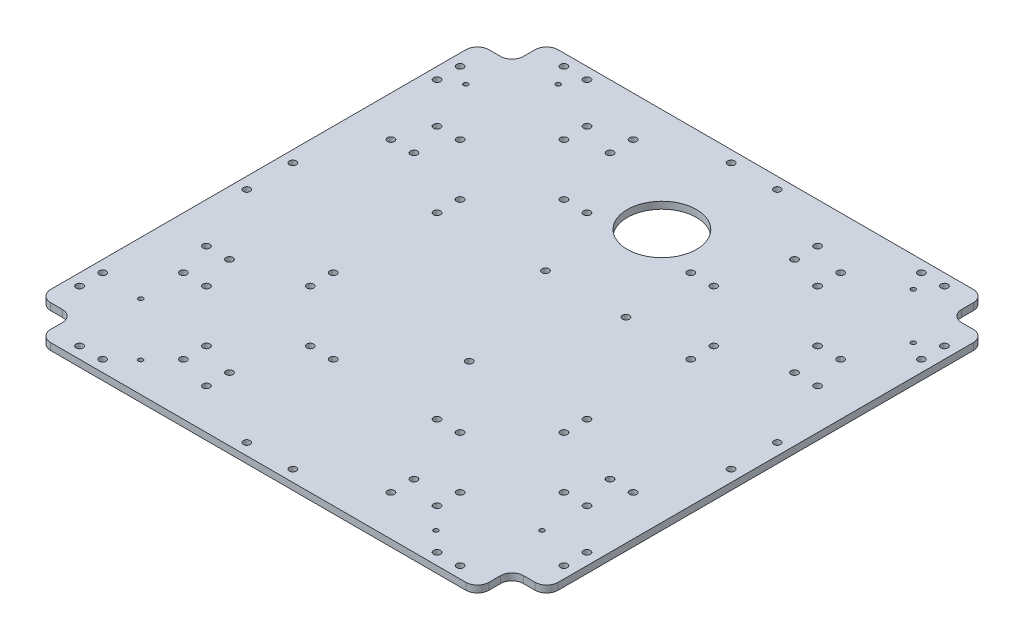
SolidWorks part; units mm, degrees
material "Polywood"
ref_plane "Спереди" through (0, 0, 0) normal (0, 0, 1) x (1, 0, 0)
ref_plane "Сверху" through (0, 0, 0) normal (0, 1, 0) x (1, 0, 0)
ref_plane "Справа" through (0, 0, 0) normal (1, 0, 0) x (0, 0, -1)
sketch "Эскиз1" plane through (0, 0, 0) normal (0, 1, 0) x (1, 0, 0)
  line L1 (110, -110) -> (-110, -110)
  line L2 (110, -110) -> (110, 110)
  line L3 (110, 110) -> (-110, 110)
  line L4 (-110, -110) -> (-110, 110)
  line L5 (110, -110) -> (-110, 110) construction
  line L6 (110, 110) -> (-110, -110) construction
  line L7 (0, 0) -> (50000, 0) construction
  circle A32 centre (0, 65) radius 15
  point P0 (0, 0)
  dimension "D6" = 30
  dimension "D2" = 220
  dimension "D1" = 220
  dimension "D7" = 65
extrude "Бобышка-Вытянуть1" add sketch "Эскиз1" along normal blind 3
sketch "Эскиз2" plane through (0, 0, 0) normal (0, 0, 1) x (1, 0, 0)
  line L0 (0, 0) -> (0, 41.9945) construction
sketch "Эскиз3" plane through (0, 3, 0) normal (0, 1, 0) x (1, 0, 0)
  line L8 (0, 0) -> (0, -50000) construction
  line L9 (0, 0) -> (50000, 0) construction
  line L28 (110, 110) -> (110, 95)
  line L29 (-110, 110) -> (-95, 110)
  line L30 (-110, 110) -> (-110, 95)
  line L31 (-110, 95) -> (-95, 95)
  line L32 (-95, 110) -> (-95, 95)
  line L33 (110, 110) -> (95, 110)
  line L34 (95, 110) -> (95, 95)
  line L35 (110, 95) -> (95, 95)
  line L36 (110, -110) -> (95, -110)
  line L37 (110, -110) -> (110, -95)
  line L38 (110, -95) -> (95, -95)
  line L39 (95, -110) -> (95, -95)
  line L40 (-110, -110) -> (-110, -95)
  line L41 (-110, -110) -> (-95, -110)
  line L42 (-95, -110) -> (-95, -95)
  line L43 (-110, -95) -> (-95, -95)
  dimension "D1" = 15
extrude "Вырез-Вытянуть1" cut sketch "Эскиз3" against normal through all
fillet "Скругление1" radius 5 4 edges at (-95, 1.5, -95) (-95, 1.5, 95) (95, 1.5, 95) (95, 1.5, -95)
fillet "Скругление2" radius 5 8 edges at (95, 1.5, -110) (110, 1.5, -95) (110, 1.5, 95) (95, 1.5, 110) (-95, 1.5, -110) (-110, 1.5, -95) (-95, 1.5, 110) (-110, 1.5, 95)
sketch "Эскиз4" plane through (0, 3, 0) normal (0, 1, 0) x (1, 0, 0)
  line L1 (90, 110) -> (-90, 110) construction
  line L2 (-110, 90) -> (-110, -90) construction
  line L3 (-77.5, 104.7863) -> (-77.5, -49895.2137) construction
  line L4 (0, 0) -> (0, 50000) construction
  circle A36 centre (-82.5, 105) radius 1.5
  circle A37 centre (-72.5, 105) radius 1.5
  circle A38 centre (72.5, 105) radius 1.5
  circle A39 centre (82.5, 105) radius 1.5
  circle A40 centre (105, 82.5) radius 1.5
  circle A41 centre (105, 72.5) radius 1.5
  circle A42 centre (105, -72.5) radius 1.5
  circle A43 centre (105, -82.5) radius 1.5
  circle A44 centre (82.5, -105) radius 1.5
  circle A45 centre (72.5, -105) radius 1.5
  circle A46 centre (-72.5, -105) radius 1.5
  circle A47 centre (-82.5, -105) radius 1.5
  circle A48 centre (-105, -82.5) radius 1.5
  circle A49 centre (-105, -72.5) radius 1.5
  circle A50 centre (-105, 72.5) radius 1.5
  circle A51 centre (-105, 82.5) radius 1.5
  circle A52 centre (-10, 105) radius 1.5
  circle A53 centre (10, 105) radius 1.5
  circle A54 centre (105, 10) radius 1.5
  circle A55 centre (105, -10) radius 1.5
  circle A56 centre (10, -105) radius 1.5
  circle A57 centre (-10, -105) radius 1.5
  circle A58 centre (-105, -10) radius 1.5
  circle A59 centre (-105, 10) radius 1.5
  dimension "D1" = 3
  dimension "D2" = 5
  dimension "D3" = 27.5
  dimension "D4" = 5
  dimension "D6" = 10
  dimension "D5" = 4
  dimension "D7" = 4
extrude "Вырез-Вытянуть2" cut sketch "Эскиз4" against normal through all
sketch "Эскиз6" plane through (0, 3, 0) normal (0, 1, 0) x (1, 0, 0)
  line L0 (7.7, 41.6342) -> (7.7, -49958.3658) construction
  line L1 (-12.75, 27.25) -> (28.15, 27.25) construction
  line L2 (-12.75, 27.25) -> (-12.75, -29.25) construction
  line L3 (-12.75, -29.25) -> (28.15, -29.25) construction
  line L4 (28.15, 27.25) -> (28.15, -29.25) construction
  circle A0 centre (-9.75, 24.25) radius 1.5
  circle A1 centre (7.7, -26.25) radius 1.5
  circle A2 centre (25.15, 24.25) radius 1.5
  point P8 (7.7, 27.25)
  point P13 (0, 0)
  dimension "D3" = 3
  dimension "D7" = 27.25
  dimension "D1" = 40.9
  dimension "D2" = 56.5
  dimension "D4" = 3
  dimension "D5" = 17.45
  dimension "D6" = 50.5
  dimension "D8" = 12.75
extrude "MTi-680G holes" cut sketch "Эскиз6" against normal through all
sketch "Sketch1" plane through (0, 3, 0) normal (0, 1, 0) x (1, 0, 0)
  line L1 (55, -55) -> (-55, -55) construction
  line L2 (55, -55) -> (55, 55) construction
  line L3 (55, 55) -> (-55, 55) construction
  line L4 (-55, -55) -> (-55, 55) construction
  line L5 (55, -55) -> (-55, 55) construction
  line L6 (55, 55) -> (-55, -55) construction
  circle A0 centre (-55, 32.5) radius 1.5
  circle A1 centre (-55, 22.5) radius 1.5
  circle A20 centre (-77.5, 55) radius 1.5
  circle A21 centre (-87.5, 55) radius 1.5
  circle A22 centre (-55, 77.5) radius 1.5
  circle A23 centre (-55, 87.5) radius 1.5
  circle A24 centre (-32.5, 55) radius 1.5
  circle A25 centre (-22.5, 55) radius 1.5
  circle A26 centre (32.5, 55) radius 1.5
  circle A27 centre (22.5, 55) radius 1.5
  circle A28 centre (55, 77.5) radius 1.5
  circle A29 centre (55, 87.5) radius 1.5
  circle A30 centre (77.5, 55) radius 1.5
  circle A31 centre (87.5, 55) radius 1.5
  circle A32 centre (55, 32.5) radius 1.5
  circle A33 centre (55, 22.5) radius 1.5
  circle A34 centre (55, -32.5) radius 1.5
  circle A35 centre (55, -22.5) radius 1.5
  circle A36 centre (77.5, -55) radius 1.5
  circle A37 centre (87.5, -55) radius 1.5
  circle A38 centre (55, -77.5) radius 1.5
  circle A39 centre (55, -87.5) radius 1.5
  circle A40 centre (32.5, -55) radius 1.5
  circle A41 centre (22.5, -55) radius 1.5
  circle A42 centre (-32.5, -55) radius 1.5
  circle A43 centre (-22.5, -55) radius 1.5
  circle A44 centre (-55, -77.5) radius 1.5
  circle A45 centre (-55, -87.5) radius 1.5
  circle A46 centre (-77.5, -55) radius 1.5
  circle A47 centre (-87.5, -55) radius 1.5
  circle A48 centre (-55, -32.5) radius 1.5
  circle A49 centre (-55, -22.5) radius 1.5
  point P0 (0, 0)
  dimension "D5" = 3
  dimension "D1" = 110
  dimension "D2" = 110
  dimension "D3" = 22.5
  dimension "D4" = 10
  dimension "D6" = 4
  dimension "D7" = 4
extrude "Column holes" cut sketch "Sketch1" against normal through all
sketch "Sketch2" plane through (0, 3, 0) normal (0, 1, 0) x (1, 0, 0)
  line L0 (-110, 90) -> (-110, -90) construction
  line L1 (90, 110) -> (-90, 110) construction
  line L2 (0, 0) -> (-35355.3391, 35355.3391) construction
  line L3 (0, 0) -> (50000, 0) construction
  line L4 (-110, 90) -> (-110, -90) construction
  line L5 (-90, -110) -> (90, -110) construction
  line L6 (-66.802, -76.802) -> (-35422.141, -35432.141) construction
  line L7 (-87, -74) -> (-87, -77) construction
  line L8 (-87, -77) -> (-67, -77) construction
  line L9 (0, 0) -> (0, -50000) construction
  circle A0 centre (-77, 97) radius 1
  circle A1 centre (-97, 77) radius 1
  circle A2 centre (77, 97) radius 1
  circle A3 centre (97, 77) radius 1
  circle A8 centre (97, -77) radius 1 [skipped]
  circle A9 centre (77, -97) radius 1 [skipped]
  circle A10 centre (-77, -97) radius 1 [skipped]
  circle A11 centre (-97, -77) radius 1 [skipped]
  circle A12 centre (-87, -74) radius 1
  circle A13 centre (-64, -97) radius 1
  circle A14 centre (64, -97) radius 1
  circle A15 centre (87, -74) radius 1
  dimension "D3" = 2
  dimension "D1" = 33
  dimension "D2" = 13
  dimension "D4" = 135
  dimension "D6" = 23
  dimension "D7" = 36
  dimension "D8" = 3
  dimension "D9" = 20
  dimension "D10" = 135
  dimension "D5" = 4
extrude "Lighting cover holes" cut sketch "Sketch2" against normal through all
sketch "Sketch3" plane through (0, 3, 0) normal (0, 1, 0) x (1, 0, 0)
  line L0 (0, 0) -> (0, -50000) construction
  line L1 (-90, -110) -> (90, -110) construction
  line L2 (-34.6501, -87.5) -> (49965.3499, -87.5) construction
  circle A0 centre (-40, -92.5) radius 1.5
  circle A1 centre (-40, -82.5) radius 1.5
  circle A2 centre (40, -82.5) radius 1.5
  circle A3 centre (40, -92.5) radius 1.5
  circle A4 centre (-92.5, 40) radius 1.5
  circle A5 centre (-82.5, 40) radius 1.5
  circle A6 centre (-82.5, -40) radius 1.5
  circle A7 centre (-92.5, -40) radius 1.5
  circle A8 centre (40, 92.5) radius 1.5
  circle A9 centre (40, 82.5) radius 1.5
  circle A10 centre (-40, 82.5) radius 1.5
  circle A11 centre (-40, 92.5) radius 1.5
  circle A12 centre (92.5, -40) radius 1.5
  circle A13 centre (82.5, -40) radius 1.5
  circle A14 centre (82.5, 40) radius 1.5
  circle A15 centre (92.5, 40) radius 1.5
  dimension "D1" = 3
  dimension "D2" = 17.5
  dimension "D3" = 5
  dimension "D4" = 40
  dimension "D5" = 4
extrude "Cut-Extrude3" cut sketch "Sketch3" against normal through all
equation "\"camera plate width\"=220"
equation "\"D2@Эскиз1\"=\"camera plate width\""
equation "\"camera plate length\"=220"
equation "\"D1@Эскиз1\"=\"camera plate length\""
